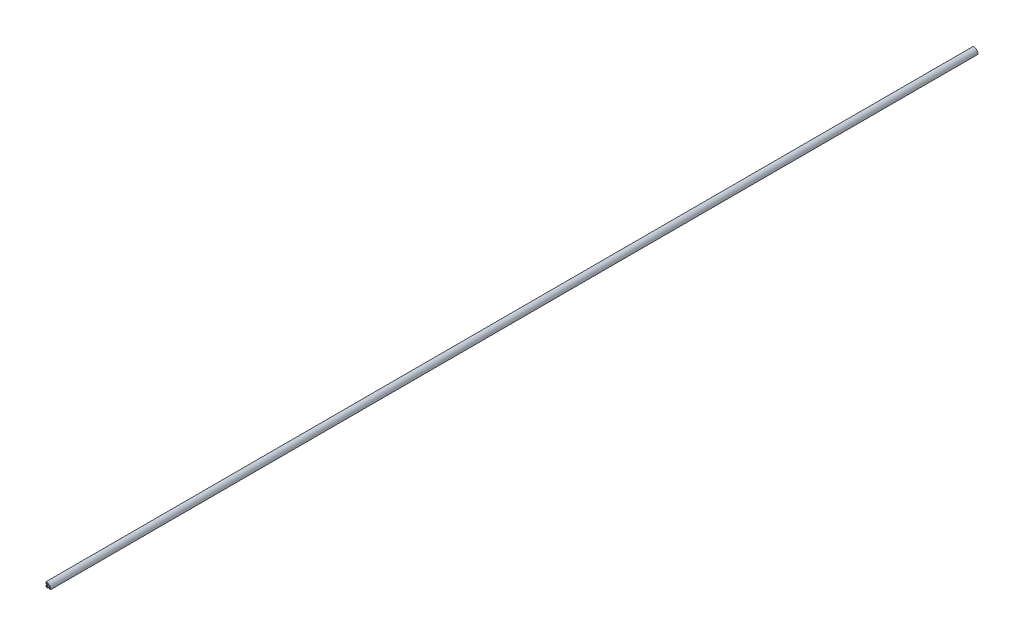
SolidWorks part; units mm, degrees
ref_plane "Front Plane" through (0, 0, 0) normal (0, 0, 1) x (1, 0, 0)
ref_plane "Top Plane" through (0, 0, 0) normal (0, 1, 0) x (1, 0, 0)
ref_plane "Right Plane" through (0, 0, 0) normal (1, 0, 0) x (0, 0, -1)
sketch "Sketch1" plane through (0, 0, 0) normal (0, 0, 1) x (1, 0, 0)
  line L44 (-11.2929, -9.1716) -> (-13, -9.1716)
  line L45 (-13, -9.1716) -> (-13, -4)
  line L46 (-13, -4) -> (-15, -4)
  line L47 (-15, -4) -> (-15, -15)
  line L48 (-15, -15) -> (-4, -15)
  line L49 (-4, -15) -> (-4, -13)
  line L50 (-4, -13) -> (-9.1716, -13)
  line L51 (-9.1716, -13) -> (-9.1716, -11.2929)
  line L52 (-9.1716, -11.2929) -> (-5.4787, -7.6)
  line L53 (-5.4787, -7.6) -> (3.2314, -7.6)
  line L54 (3.2314, -7.6) -> (7.2657, -11.6343)
  line L55 (7.2657, -11.6343) -> (7.2657, -13)
  line L56 (7.2657, -13) -> (4, -13)
  line L57 (4, -13) -> (4, -15)
  line L58 (4, -15) -> (15.0015, -15)
  line L59 (-15, 15.0015) -> (-15, 4)
  line L60 (-15, 4) -> (-13, 4)
  line L61 (-13, 4) -> (-13, 7.2657)
  line L62 (-13, 7.2657) -> (-11.6343, 7.2657)
  line L63 (-11.6343, 7.2657) -> (-7.6, 3.2314)
  line L64 (-7.6, 3.2314) -> (-7.6, -5.4787)
  line L65 (-7.6, -5.4787) -> (-11.2929, -9.1716)
  circle A1 centre (0, 0) radius 6.05
  arc A2 (15.0015, -15) -> (-15, 15.0015) centre (-15, -15) ccw
extrude "Extrude1" add sketch "Sketch1" against normal blind 6000
sketch "Sketch2" plane through (0, 0, 0) normal (0, 0, 1) x (1, 0, 0)
  line L0 (6.05, 0) -> (8.0224, 0)
  line L1 (0, 6.05) -> (0, 7.9797)
  line L2 (-5.2593, 2.9904) -> (-10.8018, 8.5329)
  line L3 (-10.8018, 8.5329) -> (-13.012, 8.5329)
  line L4 (-13.012, 8.5329) -> (-13.012, 12.4815)
  line L5 (2.8217, -5.3517) -> (8.5196, -11.0495)
  line L6 (8.5196, -11.0495) -> (8.5196, -12.9457)
  line L7 (8.5196, -12.9457) -> (12.4344, -12.9457)
  arc A0 (-13.012, 12.4815) -> (0, 7.9797) centre (-13.012, -8.5746) cw
  circle A1 centre (0, 0) radius 6.05 construction
  arc A2 (12.4344, -12.9457) -> (8.0224, 0) centre (-8.7642, -12.9457) ccw
  arc A3 (-5.2593, 2.9904) -> (2.8217, -5.3517) centre (0, 0) ccw
  arc A4 (6.05, 0) -> (0, 6.05) centre (0, 0) ccw
extrude "Cut-Extrude1" cut sketch "Sketch2" against normal through all
